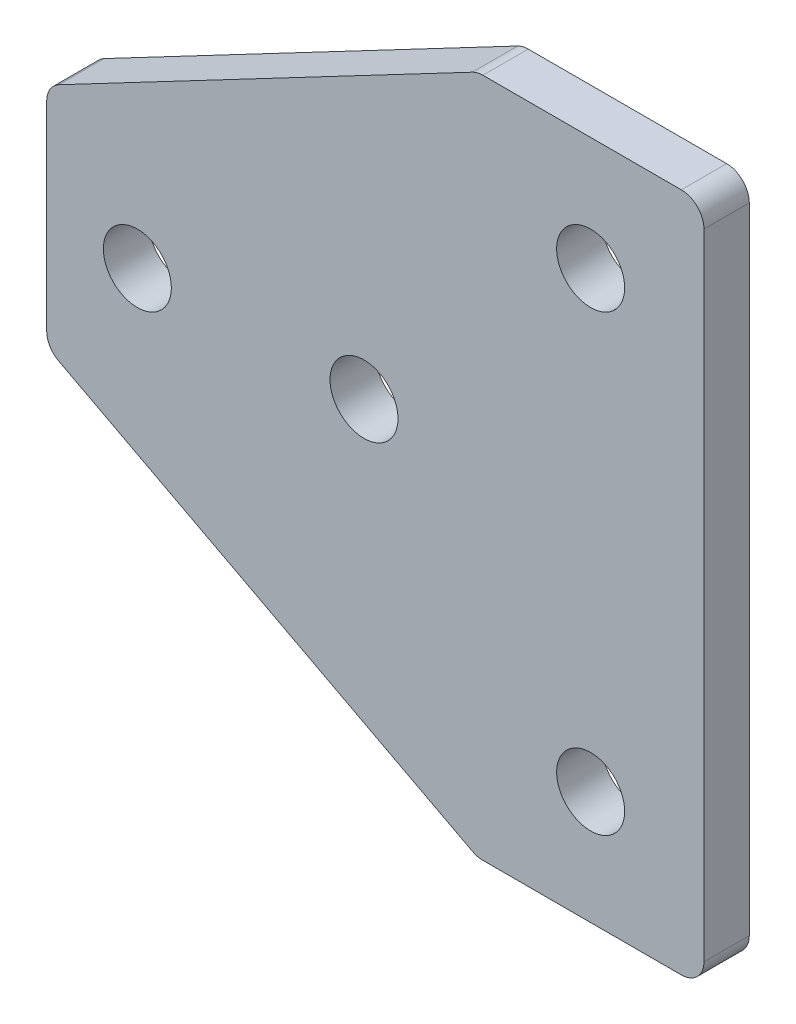
SolidWorks part; units mm, degrees
material "环氧板3240"
ref_plane "前视基准面" through (0, 0, 0) normal (0, 0, 1) x (1, 0, 0)
ref_plane "上视基准面" through (0, 0, 0) normal (0, 1, 0) x (1, 0, 0)
ref_plane "右视基准面" through (0, 0, 0) normal (1, 0, 0) x (0, 0, -1)
other "Configuration Table"
sketch "草图1" plane through (0, 0, 0) normal (0, 0, 1) x (1, 0, 0)
  line L0 (0, 15) -> (0, -15)
  line L1 (0, -15) -> (-10, -15)
  line L2 (-10, -15) -> (-29, -5)
  line L5 (-29, 5) -> (-10, 15)
  line L6 (-10, 15) -> (0, 15)
  line L7 (0, 0) -> (-29, 0) construction
  line L8 (-5, 15) -> (-5, -15) construction
  line L10 (-29, 5) -> (-29, -5)
  circle A1 centre (-15, 0) radius 1.5
  circle A4 centre (-5, -10) radius 1.5
  circle A5 centre (-5, 10) radius 1.5
  circle A6 centre (-25, 0) radius 1.5
  dimension "D3" = 3
  dimension "D5" = 10
  dimension "D6" = 20
  dimension "D7" = 10
  dimension "D1" = 10
  dimension "D2" = 10
  dimension "D4" = 30
  dimension "D8" = 4
  dimension "D9" = 29
extrude "凸台-拉伸1" add sketch "草图1" along normal blind 2
fillet "圆角1" radius 1 6 edges at (0, -15, 1) (-10, -15, 1) (0, 15, 1) (-10, 15, 1) (-29, -5, 1) (-29, 5, 1)
